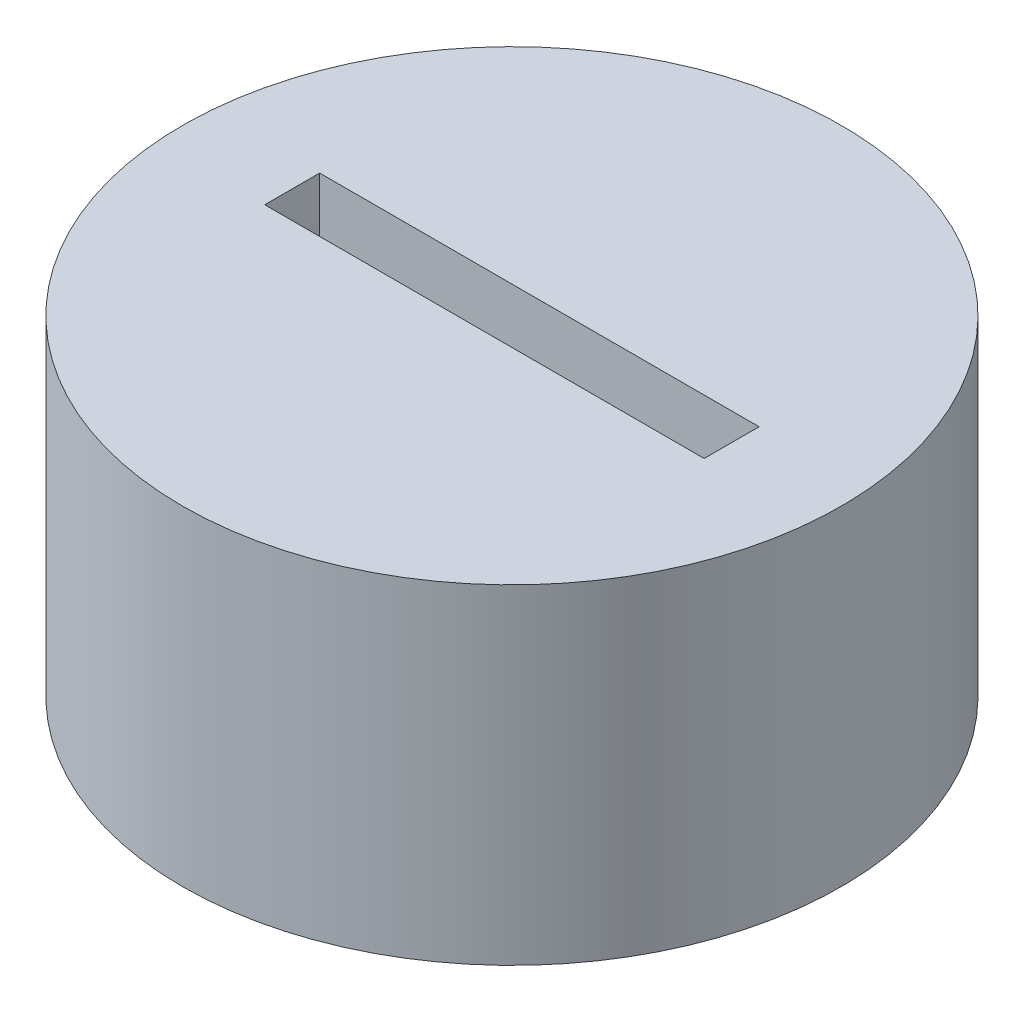
SolidWorks part; units mm, degrees
ref_plane "Ebene vorne" through (0, 0, 0) normal (0, 0, 1) x (1, 0, 0)
ref_plane "Ebene oben" through (0, 0, 0) normal (0, 1, 0) x (1, 0, 0)
ref_plane "Ebene rechts" through (0, 0, 0) normal (1, 0, 0) x (0, 0, -1)
sketch "Skizze1" plane through (0, 0, 0) normal (0, 1, 0) x (1, 0, 0)
  circle A0 centre (0, 0) radius 6
  dimension "D1" = 12
extrude "Aufsatz-Linear austragen1" add sketch "Skizze1" along normal blind 6
cosmetic thread "Gewindedarstellung1" parameters "D2"=10.619
sketch "Skizze2" plane through (0, 6, 0) normal (0, 1, 0) x (1, 0, 0)
  line L1 (-4, -0.5) -> (4, -0.5)
  line L2 (-4, -0.5) -> (-4, 0.5)
  line L3 (-4, 0.5) -> (4, 0.5)
  line L4 (4, -0.5) -> (4, 0.5)
  line L5 (-4, -0.5) -> (4, 0.5) construction
  line L6 (-4, 0.5) -> (4, -0.5) construction
  point P0 (0, 0)
  dimension "D1" = 1
  dimension "D2" = 8
extrude "Schnitt-Linear austragen1" cut sketch "Skizze2" against normal blind 1.5
sketch "Skizze3" plane through (0, 0, 0) normal (0, -1, 0) x (1, 0, 0)
  line L1 (-0.5, 4) -> (0.5, 4)
  line L2 (-0.5, 4) -> (-0.5, -4)
  line L3 (-0.5, -4) -> (0.5, -4)
  line L4 (0.5, 4) -> (0.5, -4)
  line L5 (-0.5, 4) -> (0.5, -4) construction
  line L6 (-0.5, -4) -> (0.5, 4) construction
  point P0 (0, 0)
  dimension "D1" = 1
  dimension "D2" = 8
extrude "Schnitt-Linear austragen2" cut sketch "Skizze3" against normal blind 1.5
